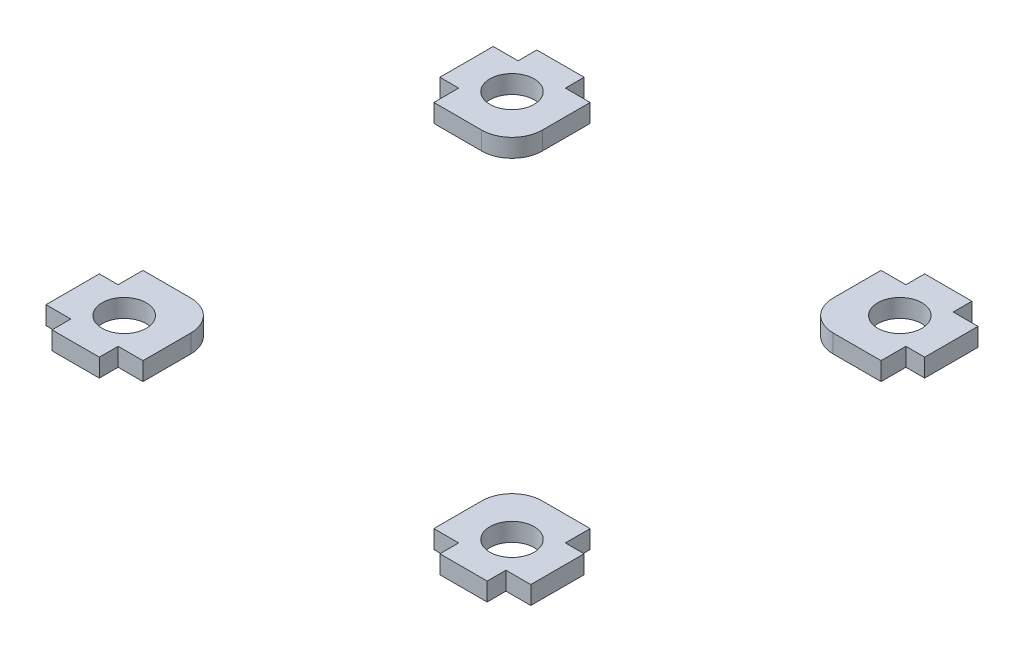
SolidWorks part; units mm, degrees
ref_plane "Front Plane" through (0, 0, 0) normal (0, 0, 1) x (1, 0, 0)
ref_plane "Top Plane" through (0, 0, 0) normal (0, 1, 0) x (1, 0, 0)
ref_plane "Right Plane" through (0, 0, 0) normal (1, 0, 0) x (0, 0, -1)
sketch "Sketch1" plane through (0, 0, 0) normal (0, 1, 0) x (1, 0, 0)
  line L0 (0, 40) -> (40, 40) construction
  line L1 (0, 0) -> (80, 0) construction
  line L2 (0, 0) -> (0, 80) construction
  line L3 (0, 80) -> (80, 80) construction
  line L4 (80, 0) -> (80, 80) construction
  line L5 (80, 0) -> (80, 80) construction
  line L6 (80, 80) -> (0, 80) construction
  line L7 (40, 40) -> (40, 80) construction
  line L8 (40, 40) -> (40, 80) construction
  line L9 (80, 40) -> (0, 40) construction
  line L10 (16, 16) -> (16, 0) construction
  line L11 (0, 0) -> (16, 0)
  line L12 (0, 0) -> (0, 16)
  line L13 (0, 16) -> (11, 16)
  line L14 (16, 0) -> (16, 11)
  line L15 (0, 16) -> (16, 16) construction
  line L16 (0, 0) -> (0, 80) construction
  line L17 (80, 0) -> (0, 0) construction
  line L18 (16, 80) -> (16, 69)
  line L19 (0, 64) -> (11, 64)
  line L20 (0, 80) -> (0, 64)
  line L21 (0, 80) -> (16, 80)
  line L22 (80, 80) -> (64, 80)
  line L23 (80, 80) -> (80, 64)
  line L24 (80, 64) -> (69, 64)
  line L25 (64, 80) -> (64, 69)
  line L26 (64, 0) -> (64, 11)
  line L27 (80, 16) -> (69, 16)
  line L28 (80, 0) -> (80, 16)
  line L29 (80, 0) -> (64, 0)
  circle A0 centre (8, 8) radius 3.65
  circle A1 centre (8, 8) radius 3.65 construction
  arc A2 (16, 69) -> (11, 64) centre (11, 69) cw
  circle A3 centre (8, 72) radius 3.65
  circle A4 centre (72, 72) radius 3.65
  arc A5 (16, 11) -> (11, 16) centre (11, 11) ccw
  arc A6 (64, 69) -> (69, 64) centre (69, 69) ccw
  arc A7 (64, 11) -> (69, 16) centre (69, 11) cw
  circle A8 centre (72, 8) radius 3.65
  point P49 (16, 16)
  dimension "D1" = 5
sketch "Sketch2" plane through (0, 0, 0) normal (0, 0, 1) x (1, 0, 0)
  line L0 (0, 0) -> (16, 0)
  line L1 (0, 0) -> (80, 0) construction
  line L2 (0, 0) -> (0, -3)
  line L3 (0, -3) -> (80, -3) construction
  line L4 (80, 0) -> (80, -3)
  line L5 (16, 0) -> (16, -3)
  line L6 (16, -3) -> (0, -3)
  line L7 (40, 0) -> (40, -3) construction
  line L8 (80, 0) -> (64, 0)
  line L9 (64, 0) -> (64, -3)
  line L10 (64, -3) -> (80, -3)
extrude "Boss-Extrude1" add sketch "Sketch1" against normal up to vertex (3 mm away) up to point (0, -3, 0)
sketch "Sketch3" plane through (0, 0, 0) normal (0, 1, 0) x (1, 0, 0)
  line L4 (16, 3) -> (12, 3)
  line L5 (12, 3) -> (12, 0)
  line L6 (12, 0) -> (16, 0)
  line L7 (16, 0) -> (16, 3)
  line L8 (16, 3) -> (12, 3) construction
  line L9 (12, 3) -> (12, 0) construction
  line L10 (12, 0) -> (16, 0) construction
  line L11 (16, 0) -> (16, 3) construction
  line L12 (3, 64) -> (3, 68)
  line L13 (3, 68) -> (0, 68)
  line L14 (0, 68) -> (0, 64)
  line L15 (0, 64) -> (3, 64)
  line L16 (3, 64) -> (3, 68) construction
  line L17 (3, 68) -> (0, 68) construction
  line L18 (0, 68) -> (0, 64) construction
  line L19 (0, 64) -> (3, 64) construction
  line L20 (80, 16) -> (77, 16)
  line L21 (80, 12) -> (80, 16)
  line L22 (77, 12) -> (80, 12)
  line L23 (77, 16) -> (77, 12)
  line L24 (80, 16) -> (77, 16) construction
  line L25 (80, 12) -> (80, 16) construction
  line L26 (77, 12) -> (80, 12) construction
  line L27 (77, 16) -> (77, 12) construction
  line L28 (80, 3) -> (76, 3)
  line L29 (80, 0) -> (80, 3)
  line L30 (76, 0) -> (80, 0)
  line L31 (76, 3) -> (76, 0)
  line L32 (80, 3) -> (76, 3) construction
  line L33 (80, 0) -> (80, 3) construction
  line L34 (76, 0) -> (80, 0) construction
  line L35 (76, 3) -> (76, 0) construction
  line L36 (4, 3) -> (0, 3)
  line L37 (4, 0) -> (4, 3)
  line L38 (0, 0) -> (4, 0)
  line L39 (0, 3) -> (0, 0)
  line L40 (4, 3) -> (0, 3) construction
  line L41 (4, 0) -> (4, 3) construction
  line L42 (0, 0) -> (4, 0) construction
  line L43 (0, 3) -> (0, 0) construction
  line L44 (0, 12) -> (3, 12)
  line L45 (0, 16) -> (0, 12)
  line L46 (3, 16) -> (0, 16)
  line L47 (3, 12) -> (3, 16)
  line L48 (0, 12) -> (3, 12) construction
  line L49 (0, 16) -> (0, 12) construction
  line L50 (3, 16) -> (0, 16) construction
  line L51 (3, 12) -> (3, 16) construction
  line L52 (68, 3) -> (64, 3)
  line L53 (68, 0) -> (68, 3)
  line L54 (64, 0) -> (68, 0)
  line L55 (64, 3) -> (64, 0)
  line L56 (68, 3) -> (64, 3) construction
  line L57 (68, 0) -> (68, 3) construction
  line L58 (64, 0) -> (68, 0) construction
  line L59 (64, 3) -> (64, 0) construction
  line L60 (76, 80) -> (76, 77)
  line L61 (80, 80) -> (76, 80)
  line L62 (80, 77) -> (80, 80)
  line L63 (76, 77) -> (80, 77)
  line L64 (76, 80) -> (76, 77) construction
  line L65 (80, 80) -> (76, 80) construction
  line L66 (80, 77) -> (80, 80) construction
  line L67 (76, 77) -> (80, 77) construction
  line L68 (64, 80) -> (64, 77)
  line L69 (68, 80) -> (64, 80)
  line L70 (68, 77) -> (68, 80)
  line L71 (64, 77) -> (68, 77)
  line L72 (64, 80) -> (64, 77) construction
  line L73 (68, 80) -> (64, 80) construction
  line L74 (68, 77) -> (68, 80) construction
  line L75 (64, 77) -> (68, 77) construction
  line L76 (16, 77) -> (16, 80)
  line L77 (16, 80) -> (12, 80)
  line L78 (12, 80) -> (12, 77)
  line L79 (12, 77) -> (16, 77)
  line L80 (16, 77) -> (16, 80) construction
  line L81 (16, 80) -> (12, 80) construction
  line L82 (12, 80) -> (12, 77) construction
  line L83 (12, 77) -> (16, 77) construction
  line L84 (4, 77) -> (4, 80)
  line L85 (4, 80) -> (0, 80)
  line L86 (0, 80) -> (0, 77)
  line L87 (0, 77) -> (4, 77)
  line L88 (4, 77) -> (4, 80) construction
  line L89 (4, 80) -> (0, 80) construction
  line L90 (0, 80) -> (0, 77) construction
  line L91 (0, 77) -> (4, 77) construction
  line L92 (80, 68) -> (77, 68)
  line L93 (77, 68) -> (77, 64)
  line L94 (77, 64) -> (80, 64)
  line L95 (80, 64) -> (80, 68)
  line L96 (80, 68) -> (77, 68) construction
  line L97 (77, 68) -> (77, 64) construction
  line L98 (77, 64) -> (80, 64) construction
  line L99 (80, 64) -> (80, 68) construction
  line L144 (16.1, 3.1) -> (11.9, 3.1)
  line L145 (11.9, 3.1) -> (11.9, -0.1)
  line L146 (11.9, -0.1) -> (16.1, -0.1)
  line L147 (16.1, -0.1) -> (16.1, 3.1)
  line L148 (3.1, 63.9) -> (3.1, 68.1)
  line L149 (3.1, 68.1) -> (-0.1, 68.1)
  line L150 (-0.1, 68.1) -> (-0.1, 63.9)
  line L151 (-0.1, 63.9) -> (3.1, 63.9)
  line L152 (80.1, 16.1) -> (76.9, 16.1)
  line L153 (76.9, 16.1) -> (76.9, 11.9)
  line L154 (76.9, 11.9) -> (80.1, 11.9)
  line L155 (80.1, 11.9) -> (80.1, 16.1)
  line L156 (80.1, 3.1) -> (75.9, 3.1)
  line L157 (75.9, 3.1) -> (75.9, -0.1)
  line L158 (75.9, -0.1) -> (80.1, -0.1)
  line L159 (80.1, -0.1) -> (80.1, 3.1)
  line L160 (4.1, 3.1) -> (-0.1, 3.1)
  line L161 (-0.1, 3.1) -> (-0.1, -0.1)
  line L162 (-0.1, -0.1) -> (4.1, -0.1)
  line L163 (4.1, -0.1) -> (4.1, 3.1)
  line L164 (-0.1, 11.9) -> (3.1, 11.9)
  line L165 (3.1, 11.9) -> (3.1, 16.1)
  line L166 (3.1, 16.1) -> (-0.1, 16.1)
  line L167 (-0.1, 16.1) -> (-0.1, 11.9)
  line L168 (68.1, 3.1) -> (63.9, 3.1)
  line L169 (63.9, 3.1) -> (63.9, -0.1)
  line L170 (63.9, -0.1) -> (68.1, -0.1)
  line L171 (68.1, -0.1) -> (68.1, 3.1)
  line L172 (75.9, 80.1) -> (75.9, 76.9)
  line L173 (75.9, 76.9) -> (80.1, 76.9)
  line L174 (80.1, 76.9) -> (80.1, 80.1)
  line L175 (80.1, 80.1) -> (75.9, 80.1)
  line L176 (63.9, 80.1) -> (63.9, 76.9)
  line L177 (63.9, 76.9) -> (68.1, 76.9)
  line L178 (68.1, 76.9) -> (68.1, 80.1)
  line L179 (68.1, 80.1) -> (63.9, 80.1)
  line L180 (16.1, 76.9) -> (16.1, 80.1)
  line L181 (16.1, 80.1) -> (11.9, 80.1)
  line L182 (11.9, 80.1) -> (11.9, 76.9)
  line L183 (11.9, 76.9) -> (16.1, 76.9)
  line L184 (4.1, 76.9) -> (4.1, 80.1)
  line L185 (4.1, 80.1) -> (-0.1, 80.1)
  line L186 (-0.1, 80.1) -> (-0.1, 76.9)
  line L187 (-0.1, 76.9) -> (4.1, 76.9)
  line L188 (80.1, 68.1) -> (76.9, 68.1)
  line L189 (76.9, 68.1) -> (76.9, 63.9)
  line L190 (76.9, 63.9) -> (80.1, 63.9)
  line L191 (80.1, 63.9) -> (80.1, 68.1)
  dimension "D1" = 0
  dimension "D2" = 0
  dimension "D3" = 0
  dimension "D4" = 0
  dimension "D5" = 0
  dimension "D6" = 0
  dimension "D7" = 0
  dimension "D8" = 0
  dimension "D9" = 0
  dimension "D10" = 0
  dimension "D11" = 0
  dimension "D12" = 0
  dimension "D13" = 0.1
extrude "Cut-Extrude1" cut sketch "Sketch3" against normal through all
